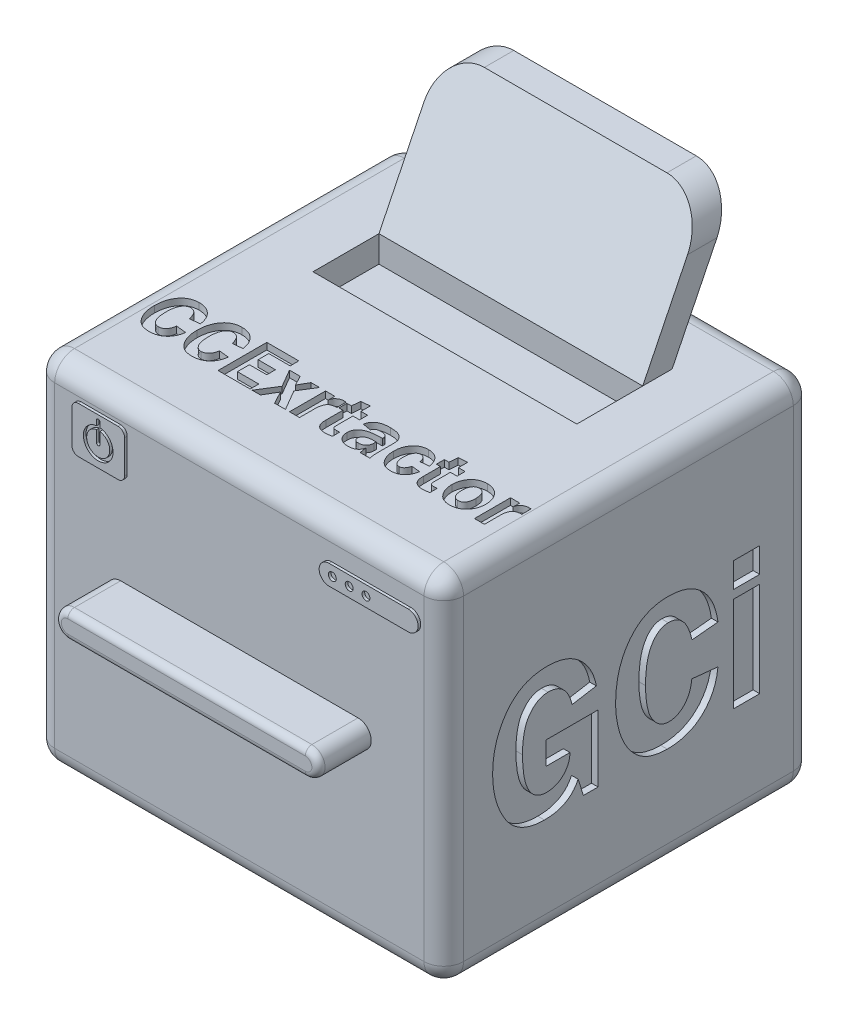
SolidWorks part; units mm, degrees
material "ABS"
ref_plane "Front" through (0, 0, 0) normal (0, 0, 1) x (1, 0, 0)
ref_plane "Top" through (0, 0, 0) normal (0, 1, 0) x (1, 0, 0)
ref_plane "Right" through (0, 0, 0) normal (1, 0, 0) x (0, 0, -1)
sketch "Sketch1" plane through (0, 0, 0) normal (0, 0, 1) x (1, 0, 0)
  line L0 (133.4483, 300.2587) -> (667.2416, 300.2587) construction
  line L2 (-196.85, 342.9) -> (196.85, 342.9)
  line L3 (-196.85, 342.9) -> (-196.85, 0)
  line L4 (-196.85, 0) -> (196.85, 0)
  line L5 (196.85, 342.9) -> (196.85, 0)
  dimension "D1" = 342.9
  dimension "D2" = 393.7
extrude "Boss-Extrude1" add sketch "Sketch1" along normal blind 355.6
sketch "Sketch2" plane through (0, 0, 355.6) normal (0, 0, 1) x (1, 0, 0)
  line L0 (196.85, 342.9) -> (-196.85, 342.9) construction
  line L1 (-158.75, 320.675) -> (-107.95, 320.675)
  line L2 (-158.75, 320.675) -> (-158.75, 276.225)
  line L3 (-158.75, 276.225) -> (-107.95, 276.225)
  line L4 (-107.95, 320.675) -> (-107.95, 276.225)
  line L5 (-158.75, 320.675) -> (-107.95, 276.225) construction
  line L6 (-158.75, 276.225) -> (-107.95, 320.675) construction
  line L7 (-196.85, 342.9) -> (-196.85, 0) construction
  point P0 (-133.35, 298.45)
  dimension "D1" = 44.45
  dimension "D2" = 63.5
  dimension "D3" = 44.45
  dimension "D4" = 50.8
extrude "Boss-Extrude2" add sketch "Sketch2" along normal blind 2.54
sketch "Sketch3" plane through (0, 0, 355.6) normal (0, 0, 1) x (1, 0, 0)
  line L0 (88.9, 298.45) -> (165.1, 298.45) construction
  line L1 (88.9, 307.975) -> (165.1, 307.975)
  line L2 (88.9, 288.925) -> (165.1, 288.925)
  line L5 (-107.95, 298.45) -> (88.9, 298.45) construction
  line L7 (-107.95, 276.225) -> (-107.95, 320.675) construction
  line L8 (196.85, 0) -> (196.85, 342.9) construction
  arc A0 (88.9, 307.975) -> (88.9, 288.925) centre (88.9, 298.45) ccw
  arc A1 (165.1, 288.925) -> (165.1, 307.975) centre (165.1, 298.45) ccw
  point P2 (127, 298.45)
  dimension "D1" = 19.05
  dimension "D2" = 76.2
  dimension "D3" = 31.75
extrude "Boss-Extrude3" add sketch "Sketch3" along normal blind 2.54
sketch "Sketch4" plane through (0, 0, 358.14) normal (0, 0, 1) x (1, 0, 0)
  line L0 (79.375, 298.45) -> (174.625, 298.45) construction
  arc A0 (88.9, 307.975) -> (88.9, 288.925) centre (88.9, 298.45) ccw construction
  arc A1 (165.1, 288.925) -> (165.1, 307.975) centre (165.1, 298.45) ccw construction
  circle A2 centre (92.075, 298.45) radius 3.81
  circle A3 centre (108.2865, 298.45) radius 3.81
  circle A4 centre (124.4979, 298.45) radius 3.81
  dimension "D1" = 7.62
  dimension "D2" = 16.2115
  dimension "D3" = 16.2115
  dimension "D4" = 12.7
extrude "Cut-Extrude1" cut sketch "Sketch4" against normal blind 2.54
sketch "Sketch5" plane through (0, 0, 355.6) normal (0, 0, 1) x (1, 0, 0)
  line L0 (-114.3, 177.8) -> (114.3, 177.8) construction
  line L1 (-114.3, 190.5) -> (114.3, 190.5)
  line L2 (-114.3, 165.1) -> (114.3, 165.1)
  line L3 (0, 177.8) -> (0, 342.9) construction
  line L4 (196.85, 342.9) -> (-196.85, 342.9) construction
  arc A0 (-114.3, 190.5) -> (-114.3, 165.1) centre (-114.3, 177.8) ccw
  arc A1 (114.3, 165.1) -> (114.3, 190.5) centre (114.3, 177.8) ccw
  point P2 (0, 177.8)
  dimension "D1" = 228.6
  dimension "D2" = 25.4
  dimension "D3" = 165.1
extrude "Boss-Extrude4" add sketch "Sketch5" along normal blind 50.8
fillet "Fillet1" radius 6.35 4 edges at (127, 177.8, 406.4) (0, 165.1, 406.4) (-127, 177.8, 406.4) (0, 190.5, 406.4)
fillet "Fillet2" radius 6.35 4 edges at (-158.75, 276.225, 356.87) (-107.95, 276.225, 356.87) (-107.95, 320.675, 356.87) (-158.75, 320.675, 356.87)
sketch "Sketch6" plane through (0, 0, 358.14) normal (0, 0, 1) x (1, 0, 0)
  line L0 (-133.35, 296.545) -> (-133.35, 276.225) construction
  line L3 (-133.35, 296.545) -> (-133.35, 315.595) construction
  line L4 (-134.9375, 296.545) -> (-134.9375, 315.595)
  line L5 (-131.7625, 296.545) -> (-131.7625, 315.595)
  line L6 (-152.4, 276.225) -> (-114.3, 276.225) construction
  circle A1 centre (-133.35, 296.545) radius 11.1125
  circle A2 centre (-133.35, 296.545) radius 14.2875
  arc A3 (-134.9375, 296.545) -> (-131.7625, 296.545) centre (-133.35, 296.545) ccw
  arc A4 (-131.7625, 315.595) -> (-134.9375, 315.595) centre (-133.35, 315.595) ccw
  point P12 (-133.35, 306.07)
  dimension "D2" = 22.225
  dimension "D3" = 3.175
  dimension "D4" = 19.05
  dimension "D5" = 20.32
  dimension "D1" = 3.175
extrude "Cut-Extrude2" cut sketch "Sketch6" against normal blind 2.54 contours L4 A2 L5 A1 | L5 A4 L4 A2 | L5 A2 L4 A1 | L4 A3 L5 A1
fillet "Fillet3" radius 19.05 12 edges at (-196.85, 171.45, 0) (-196.85, 171.45, 355.6) (196.85, 171.45, 0) (196.85, 171.45, 355.6) (0, 0, 0) (0, 0, 355.6) (0, 342.9, 0) (0, 342.9, 355.6) (-196.85, 342.9, 177.8) (196.85, 0, 177.8) (-196.85, 0, 177.8) (196.85, 342.9, 177.8)
sketch "Sketch7" plane through (0, 0, 0) normal (1, 0, 0) x (0, 0, -1)
  line L0 (-65.8773, 342.9) -> (-3.487, 469.9)
  line L1 (-336.55, 342.9) -> (-19.05, 342.9) construction
  line L2 (-94.1768, 342.9) -> (-31.7865, 469.9)
  line L3 (-31.7865, 469.9) -> (-3.487, 469.9)
  line L4 (-94.1768, 342.9) -> (-65.8773, 342.9)
  dimension "D1" = 25.4
  dimension "D2" = 127
extrude "Boss-Extrude5" add sketch "Sketch7" along normal mid plane 254
fillet "Fillet4" radius 39.116 2 edges at (-127, 469.9, 17.6368) (127, 469.9, 17.6368)
sketch "Sketch8" plane through (0, 342.9, 0) normal (0, 1, 0) x (1, 0, 0)
  line L0 (0, -94.1768) -> (0, -125.9268) construction
  line L1 (127, -94.1768) -> (-127, -94.1768) construction
  line L3 (-127, -157.6768) -> (127, -157.6768)
  line L4 (-127, -157.6768) -> (-127, -94.1768)
  line L5 (-127, -94.1768) -> (127, -94.1768)
  line L6 (127, -157.6768) -> (127, -94.1768)
  line L7 (-127, -157.6768) -> (127, -94.1768) construction
  line L8 (-127, -94.1768) -> (127, -157.6768) construction
  dimension "D1" = 63.5
  dimension "D2" = 254
extrude "Cut-Extrude3" cut sketch "Sketch8" against normal blind 25.4
extrude "Cut-Extrude4" cut sketch "Sketch9" against normal blind 6.35
sketch "Sketch9" plane through (-117.5646, 342.9, -186.1891) normal (0, 1, 0) x (1, 0, 0)
  text T0 "CCExrtactor" font "Franklin Gothic Medium" height in points 190
  point P1 (-40.9161, -495.2316)
  point P2 (-60.2354, -496.1711)
extrude "Cut-Extrude5" cut sketch "Sketch10" against normal blind 6.35
sketch "Sketch10" plane through (196.85, -12.9468, -186.1891) normal (1, 0, 0) x (0, 0, -1)
  text T0 "GCi" font "Franklin Gothic Medium" height in points 500
  point P1 (-455.4649, 142.0562)
  point P2 (-477.7987, 134.9843)
equation "\"D3@Sketch4\"=\"D2@Sketch4\""
